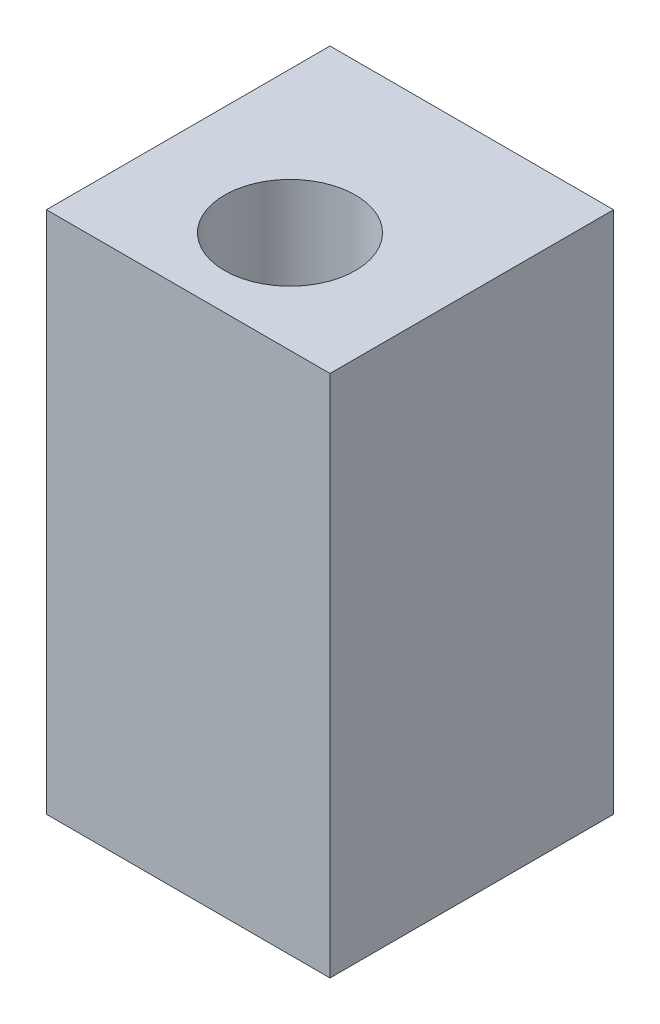
SolidWorks part; units mm, degrees
ref_plane "Front Plane" through (0, 0, 0) normal (0, 0, 1) x (1, 0, 0)
ref_plane "Top Plane" through (0, 0, 0) normal (0, 1, 0) x (1, 0, 0)
ref_plane "Right Plane" through (0, 0, 0) normal (1, 0, 0) x (0, 0, -1)
sketch "Sketch2" plane through (0, 0, 0) normal (0, 1, 0) x (1, 0, 0)
  line L1 (-4.875, 4.875) -> (4.875, 4.875)
  line L2 (-4.875, 4.875) -> (-4.875, -4.875)
  line L3 (-4.875, -4.875) -> (4.875, -4.875)
  line L4 (4.875, 4.875) -> (4.875, -4.875)
  line L5 (-4.875, 4.875) -> (4.875, -4.875) construction
  line L6 (-4.875, -4.875) -> (4.875, 4.875) construction
  point P0 (0, 0)
  dimension "D1" = 9.75
  dimension "D2" = 9.75
extrude "Boss-Extrude1" add sketch "Sketch2" along normal blind 18
sketch "Sketch3" plane through (0, 18, 0) normal (0, 1, 0) x (1, 0, 0)
  line L1 (-4.875, 4.875) -> (4.875, 4.875)
  line L2 (-4.875, 4.875) -> (-4.875, -4.875)
  line L3 (-4.875, -4.875) -> (4.875, -4.875)
  line L4 (4.875, 4.875) -> (4.875, -4.875)
  line L5 (-4.875, 4.875) -> (4.875, -4.875) construction
  line L6 (-4.875, -4.875) -> (4.875, 4.875) construction
  circle A0 centre (0, -1.375) radius 2.25
  point P0 (0, 0)
  dimension "D1" = 3.5
extrude "Cut-Extrude1" cut sketch "Sketch3" against normal blind 21 contours A0
